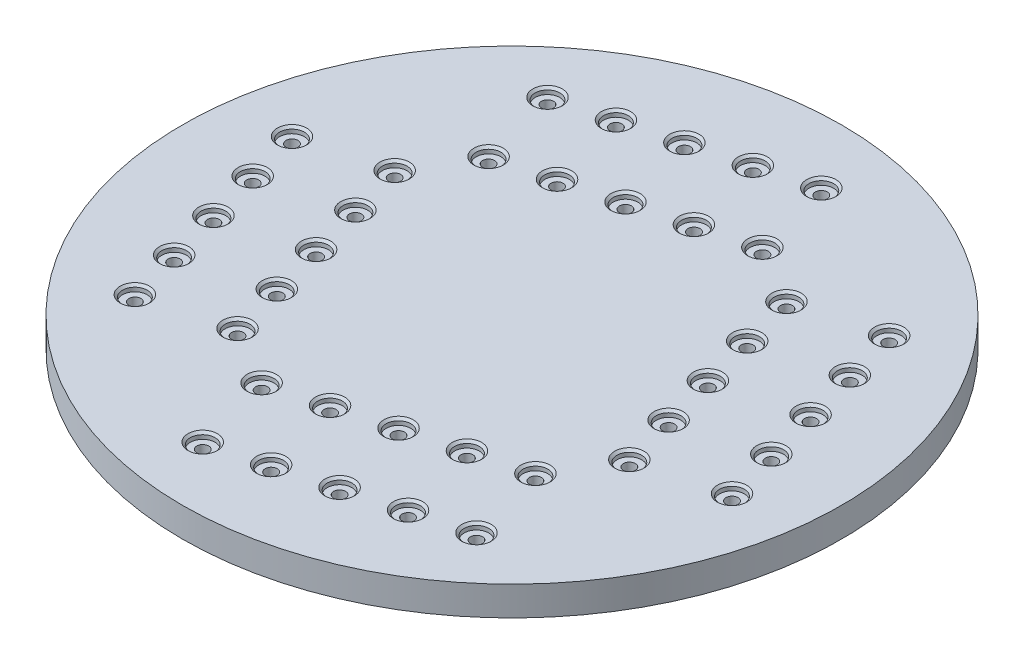
SolidWorks part; units mm, degrees
ref_plane "Front Plane" through (0, 0, 0) normal (0, 0, 1) x (1, 0, 0)
ref_plane "Top Plane" through (0, 0, 0) normal (0, 1, 0) x (1, 0, 0)
ref_plane "Right Plane" through (0, 0, 0) normal (1, 0, 0) x (0, 0, -1)
sketch "Sketch1" plane through (0, 0, 0) normal (0, 1, 0) x (1, 0, 0)
  circle A0 centre (-69.0467, 32.6186) radius 90
  dimension "D1" = 180
extrude "Boss-Extrude1" add sketch "Sketch1" along normal blind 8
hole_wizard "CBORE for #4 Binding Head Machine Screw1" [suppressed] positions "Sketch7" profile "Sketch9" counterbore size "#4" standard "ANSI Inch"
sketch "Sketch7" plane through (0, 8, 0) normal (0, 1, 0) x (1, 0, 0)
  point P2 (-28.1786, 20.1666)
  point P5 (-43.6106, 6.1987)
  point P17 (-43.3584, 66.756)
  point P23 (-64.057, 68.9518)
  point P26 (-94.4827, 59.0384)
  point P38 (-94.7349, -1.5189)
  point P41 (-109.9147, 45.0705)
  point P47 (-74.0364, -3.7146)
sketch "Sketch9" plane through (-28.1786, 8, -20.1666) normal (1, 0, 0) x (0, 0, 1)
  line L0 (0, 0) -> (0, 8)
  line L1 (0, 8) -> (1.632, 8)
  line L3 (1.632, 8) -> (1.6319, 1.7272)
  line L4 (3.3731, 1.7272) -> (1.6319, 1.7272)
  line L5 (3.3731, 1.7272) -> (3.3731, 0.5328)
  line L6 (3.3731, 0.5328) -> (4.0081, 0)
  line L7 (4.0081, 0) -> (0, 0)
  line L8 (-3.3731, 0.5328) -> (-4.0081, 0) construction
  line L11 (0, -6.35) -> (0, 107.95) construction
  dimension "Thru Hole Dia." = 3.2639
  dimension "Thru Hole Depth" = 8
  dimension "C'Bore Dia." = 6.7462
  dimension "C'Bore Depth" = 1.7272
  dimension "Near C'Sink Dia." = 8.0162
  dimension "Near C'Sink Angle" = 100
hole_wizard "CBORE for #4 Binding Head Machine Screw2" positions "Sketch10" profile "Sketch11" counterbore size "#4" standard "ANSI Inch" end condition through all
sketch "Sketch10" plane through (0, 8, 0) normal (0, 1, 0) x (1, 0, 0)
  line L0 (-81.2405, -39.6572) -> (-87.2147, -17.5917)
  point P2 (-81.2405, -39.6572)
  point P7 (-87.2147, -17.5917)
sketch "Sketch11" plane through (-81.2405, 8, 39.6572) normal (1, 0, 0) x (0, 0, 1)
  line L0 (0, 0) -> (0, 8)
  line L1 (0, 8) -> (1.632, 8)
  line L3 (1.632, 8) -> (1.632, 1.7272)
  line L4 (3.3731, 1.7272) -> (1.632, 1.7272)
  line L5 (3.3731, 1.7272) -> (3.3731, 0.635)
  line L6 (3.3731, 0.635) -> (4.0081, 0)
  line L7 (4.0081, 0) -> (0, 0)
  line L8 (-3.3731, 0.635) -> (-4.0081, 0) construction
  line L11 (0, -6.35) -> (0, 107.95) construction
  dimension "Thru Hole Dia." = 3.2639
  dimension "Thru Hole Depth" = 8
  dimension "C'Bore Dia." = 6.7462
  dimension "C'Bore Depth" = 1.7272
  dimension "Near C'Sink Dia." = 8.0162
  dimension "Near C'Sink Angle" = 90
pattern_linear "LPattern1" count 5 spacing 15.24 along (0.9652, 0, -0.2613) of "CBORE for #4 Binding Head Machine Screw2"
pattern_circular "CirPattern1" count 4 over 360 about axis through (-69.0467, 0, -32.6186) along (0, 1, 0) of "LPattern1", "CBORE for #4 Binding Head Machine Screw2"
